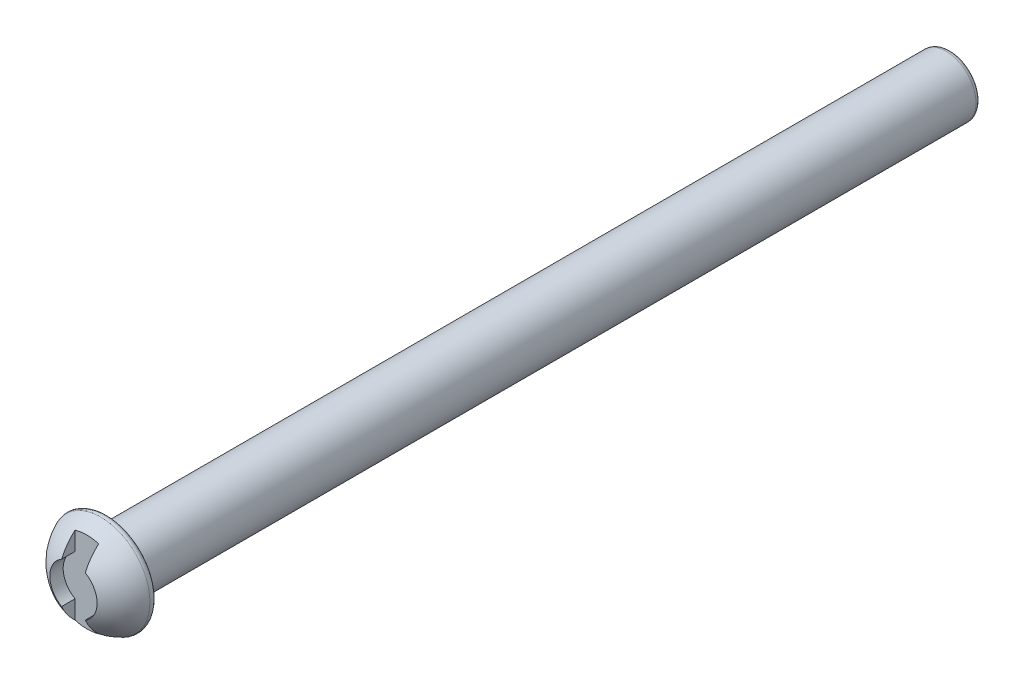
SolidWorks part; units mm, degrees
ref_plane "Front Plane" through (0, 0, 0) normal (0, 0, 1) x (1, 0, 0)
ref_plane "Top Plane" through (0, 0, 0) normal (0, 1, 0) x (1, 0, 0)
ref_plane "Right Plane" through (0, 0, 0) normal (1, 0, 0) x (0, 0, -1)
sketch "Sketch1" plane through (0, 0, 0) normal (1, 0, 0) x (0, 0, -1)
  line L0 (0, 0) -> (140, 0)
  line L1 (140, 0) -> (140, 4.75)
  line L2 (140, 4.75) -> (6.25, 4.75)
  line L3 (6.25, 4.75) -> (6.25, 8.15)
  arc A0 (6.25, 8.15) -> (0, 0) centre (8.4388, 0) ccw
  point P7 (6.25, 8.15)
  point P8 (0, 0)
  point P9 (0, 0)
  dimension "D1" = 4.75
  dimension "D2" = 140
  dimension "D3" = 8.15
  dimension "D4" = 6.25
revolve "Revolve1" add sketch "Sketch1" angle 360 about L0
ref_plane "Plane1" through (0, 0, 0) normal (0, 0, 1) x (1, 0, 0)
sketch "Sketch2" plane through (0, 0, 0) normal (0, 0, 1) x (1, 0, 0)
  line L0 (-1.875, 3.2476) -> (-1.875, 12.5581)
  line L1 (-1.875, -12.5581) -> (1.875, -12.5581)
  line L2 (-1.875, -12.5581) -> (-1.875, -3.2476)
  line L3 (-1.875, 12.5581) -> (1.875, 12.5581)
  line L4 (1.875, -12.5581) -> (1.875, -3.2476)
  line L5 (-1.875, -12.5581) -> (1.875, 12.5581) construction
  line L6 (-1.875, 12.5581) -> (1.875, -12.5581) construction
  line L7 (1.875, 3.2476) -> (1.875, 12.5581)
  arc A1 (-1.875, 3.2476) -> (-1.875, -3.2476) centre (0, 0) ccw
  arc A3 (1.875, -3.2476) -> (1.875, 3.2476) centre (0, 0) ccw
  point P0 (0, 0)
  dimension "D1" = 3.75
fillet "Fillet1" radius 0.75 2 edges at (4.75, 0, -140) (8.15, 0, -6.25)
sketch "Sketch4" plane through (0, 0, 0) normal (0, 0, 1) x (1, 0, 0)
  line L0 (1.875, -3.2476) -> (1.875, -9.3292)
  line L1 (-1.875, 9.3292) -> (1.875, 9.3292)
  line L2 (-1.875, 9.3292) -> (-1.875, 3.2476)
  line L3 (-1.875, -9.3292) -> (1.875, -9.3292)
  line L4 (1.875, 9.3292) -> (1.875, 3.2476)
  line L5 (-1.875, 9.3292) -> (1.875, -9.3292) construction
  line L6 (-1.875, -9.3292) -> (1.875, 9.3292) construction
  line L7 (-1.875, -3.2476) -> (-1.875, -9.3292)
  arc A0 (-1.875, 3.2476) -> (-1.875, -3.2476) centre (0, 0) ccw
  arc A1 (1.875, -3.2476) -> (1.875, 3.2476) centre (0, 0) ccw
  point P0 (0, 0)
  dimension "D1" = 7.5
  dimension "D2" = 3.75
extrude "Cut-Extrude6" cut sketch "Sketch4" against normal blind 3
